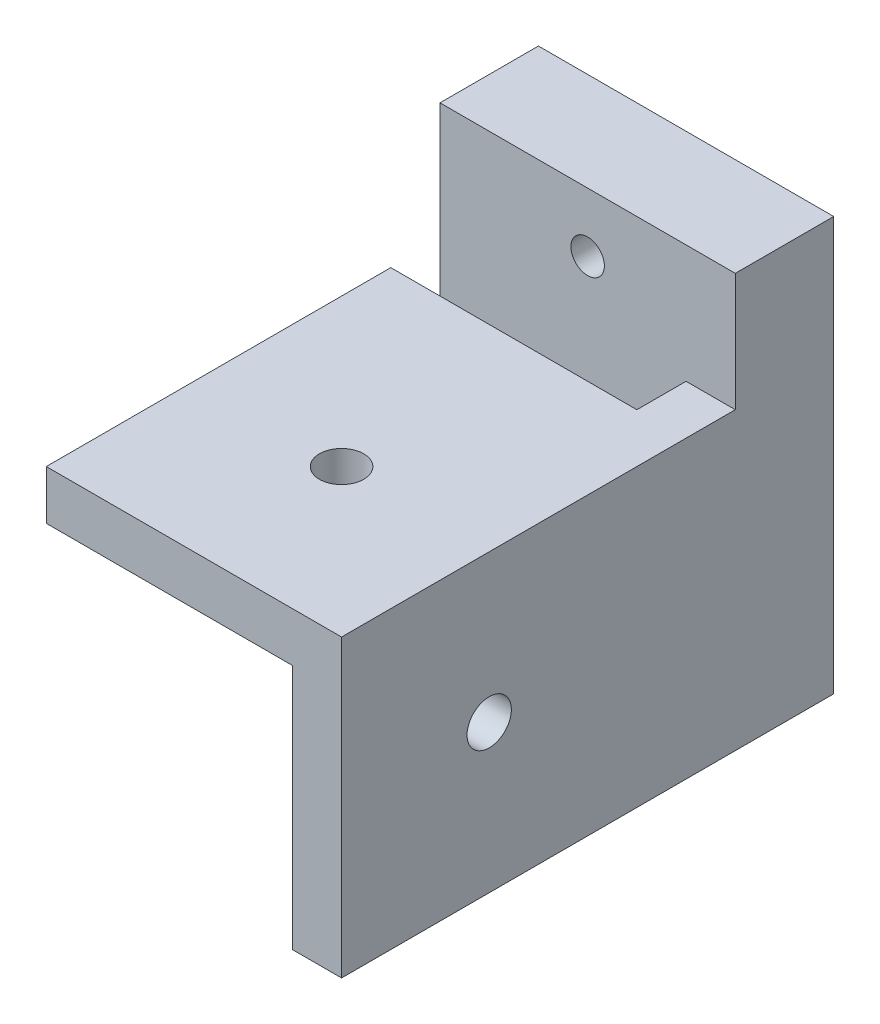
SolidWorks part; units mm, degrees
material "ABS"
ref_plane "Plano frontal" through (0, 0, 0) normal (0, 0, 1) x (1, 0, 0)
ref_plane "Plano superior" through (0, 0, 0) normal (0, 1, 0) x (1, 0, 0)
ref_plane "Plano direito" through (0, 0, 0) normal (1, 0, 0) x (0, 0, -1)
sketch "Esboço1" plane through (0, 0, 0) normal (0, 0, 1) x (1, 0, 0)
  line L9 (0, 0) -> (-30, 0)
  line L10 (0, 0) -> (0, 30)
  line L11 (0, 30) -> (-30, 30)
  line L12 (-30, 0) -> (-30, 30)
  dimension "D1" = 30
  dimension "D2" = 30
extrude "Ressalto-extrusão1" add sketch "Esboço1" along normal blind 50
sketch "Esboço2" plane through (0, 30, 0) normal (0, 1, 0) x (1, 0, 0)
  line L0 (-30, -50) -> (-30, 0) construction
  line L1 (-30, -10) -> (-5, -10)
  line L2 (-30, -10) -> (-30, -15)
  line L3 (-30, -15) -> (-5, -15)
  line L4 (-5, -10) -> (-5, -15)
  line L5 (0, 0) -> (-30, 0) construction
  line L6 (0, -50) -> (0, 0) construction
  dimension "D1" = 10
  dimension "D2" = 5
  dimension "D3" = 5
extrude "Corte-extrusão1" cut sketch "Esboço2" against normal through all
sketch "Esboço3" plane through (0, 30, 0) normal (0, 1, 0) x (1, 0, 0)
  line L0 (0, -50) -> (0, 0) construction
  line L1 (-5, -25) -> (-30, -25)
  line L2 (-5, -25) -> (-5, -50)
  line L3 (-5, -50) -> (-30, -50)
  line L4 (-30, -25) -> (-30, -50)
  line L5 (-30, -15) -> (-5, -15) construction
  dimension "D1" = 5
  dimension "D2" = 10
extrude "Corte-extrusão2" cut sketch "Esboço3" against normal through all from offset 5 offset against normal yes
hole_wizard "Furo com folga de M41" positions "3DSketch1" profile "Esboço4" hole size "M4" standard "ISO" end condition through all
sketch3d "3DSketch1"
  line L1 (-5, 0, 25) -> (-5, 25, 25) construction
  line L3 (-5, 25, 50) -> (-5, 25, 25) construction
  line L4 (-5, 25, 25) -> (-30, 25, 25) construction
  point P2 (-5, 15, 35)
  point P15 (-15, 25, 35)
  dimension "D1" = 10
  dimension "D2" = 10
  dimension "D3" = 10
  dimension "D4" = 10
sketch "Esboço4" plane through (-5, 15, 35) normal (0, 1, 0) x (0, 0, 1)
  line L0 (0, 0) -> (0, 5)
  line L1 (0, 5) -> (2.25, 5)
  line L2 (2.25, 5) -> (2.25, 0)
  line L5 (2.25, 0) -> (0, 0)
  line L11 (0, -6.35) -> (0, 107.95) construction
  dimension "Thru Hole Dia." = 4.5
  dimension "Thru Hole Depth" = 5
sketch "Esboço5" plane through (0, 30, 0) normal (0, 1, 0) x (1, 0, 0)
  line L0 (-5, -10) -> (-30, -10) construction
  line L1 (-30, 0) -> (0, 0)
  line L2 (-30, 0) -> (-30, -10)
  line L3 (-30, -10) -> (0, -10)
  line L4 (0, 0) -> (0, -10)
  line L5 (0, -50) -> (0, 0) construction
extrude "Ressalto-extrusão2" add sketch "Esboço5" along normal blind 12
hole_wizard "Rebaixo para parafuso com cabeça panela de M31" positions "Esboço8" profile "Esboço9" counterbore size "M3" standard "ISO" end condition through all
sketch "Esboço8" plane through (0, 0, 0) normal (0, 0, -1) x (-1, 0, 0)
  line L0 (15, 42) -> (15, 36) construction
  line L1 (0, 42) -> (30, 42) construction
  point P0 (15, 36)
  dimension "D1" = 6
sketch "Esboço9" plane through (-15, 36, 0) normal (1, 0, 0) x (0, 1, 0)
  line L0 (0, 0) -> (0, 50)
  line L1 (0, 50) -> (1.7, 50)
  line L3 (1.7, 50) -> (1.7, 2.4)
  line L4 (1.7, 2.4) -> (3.5, 2.4)
  line L5 (3.5, 2.4) -> (3.5, 0)
  line L7 (3.5, 0) -> (0, 0)
  line L11 (0, -6.35) -> (0, 107.95) construction
  dimension "Thru Hole Dia." = 3.4
  dimension "Thru Hole Depth" = 50
  dimension "C'Bore Dia." = 7
  dimension "C'Bore Depth" = 2.4
